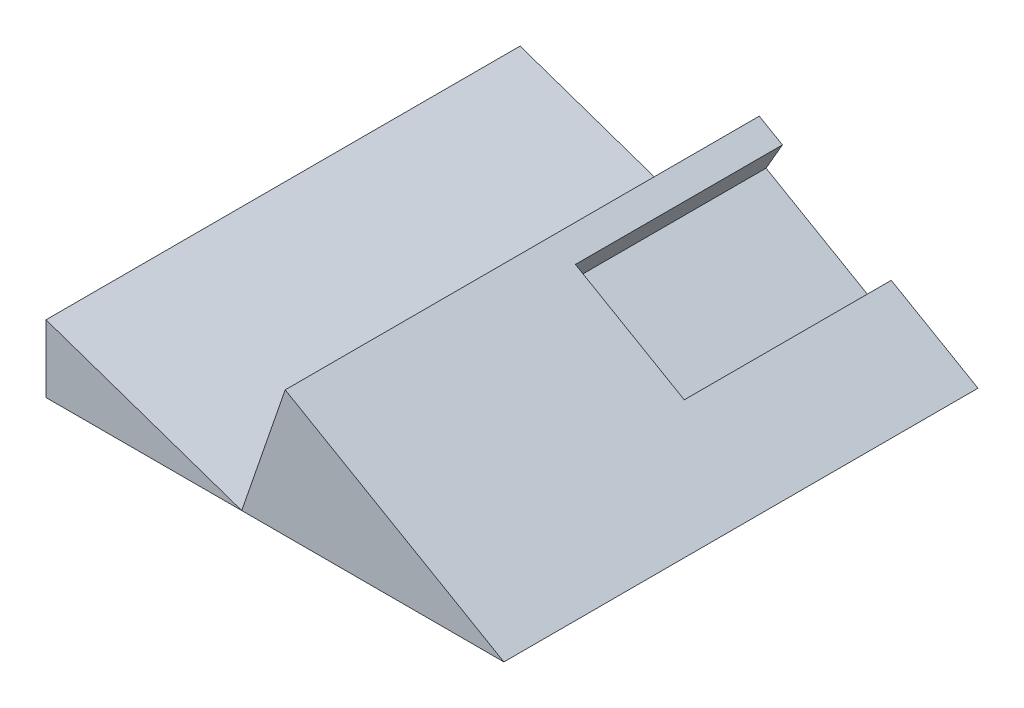
SolidWorks part; units mm, degrees
ref_plane "Front Plane" through (0, 0, 0) normal (0, 0, 1) x (1, 0, 0)
ref_plane "Top Plane" through (0, 0, 0) normal (0, 1, 0) x (1, 0, 0)
ref_plane "Right Plane" through (0, 0, 0) normal (1, 0, 0) x (0, 0, -1)
sketch "Sketch1" plane through (0, 0, 0) normal (0, 1, 0) x (1, 0, 0)
  line L1 (15, -51.5) -> (-15, -51.5)
  line L2 (15, -51.5) -> (15, 51.5)
  line L3 (15, 51.5) -> (-15, 51.5)
  line L4 (-15, -51.5) -> (-15, 51.5)
  line L5 (15, -51.5) -> (-15, 51.5) construction
  line L6 (15, 51.5) -> (-15, -51.5) construction
  point P0 (0, 0)
  dimension "D1" = 103
  dimension "D2" = 30
extrude "Boss-Extrude1" add sketch "Sketch1" along normal blind 2
sketch "Sketch2" plane through (0, 0, 51.5) normal (0, 0, 1) x (1, 0, 0)
  line L0 (15, 2) -> (-35.2295, 31)
  line L1 (0, 2) -> (0, 0)
  line L2 (0, 0) -> (18.4641, 0)
  line L3 (15, 2) -> (18.4641, 0)
  line L8 (-53.5765, 12.0888) -> (-47.0676, 31) construction
  line L9 (-47.0676, 31) -> (-17.7552, 20.9112)
  line L10 (-17.7552, 20.9112) -> (-24.2641, 2) construction
  line L11 (-24.2641, 2) -> (-53.5765, 12.0888)
  line L12 (-15, 2) -> (15, 2) construction
  line L13 (-53.5765, 12.0888) -> (-53.5765, 0)
  line L14 (-24.2641, 2) -> (-49.8195, 2) construction
  line L17 (-15, 2) -> (-15, 0)
  line L18 (-53.5765, 0) -> (-15, 0)
  line L19 (-15, 2) -> (0, 2)
  line L20 (-56.2053, 2) -> (-56.2053, 31) construction
  line L21 (-17.7552, 20.9112) -> (-24.2641, 2)
  line L22 (-56.2053, 31) -> (-14.2536, 31) construction
  dimension "D1" = 30
  dimension "D2" = 20
  dimension "D3" = 31
  dimension "D4" = 29
extrude "Boss-Extrude2" add sketch "Sketch2" against normal blind 103
sketch "Sketch6" plane through (4.616, 7.9952, 0) normal (0.5, 0.866, 0) x (0.866, -0.5, 0)
  line L0 (-21.8321, -11.5) -> (-21.8321, 58.5)
  line L1 (-21.8321, 58.5) -> (-3.0096, 58.5)
  line L2 (-3.0096, 58.5) -> (-3.0096, -11.5)
  line L3 (-3.0096, -11.5) -> (-21.8321, -11.5)
  line L4 (11.9904, -51.5) -> (-25.8321, -51.5) construction
  line L5 (-25.8321, 51.5) -> (-25.8321, -51.5) construction
  line L6 (11.9904, -51.5) -> (11.9904, 51.5) construction
  dimension "D1" = 70
  dimension "D2" = 40
  dimension "D3" = 4
  dimension "D4" = 15
extrude "Cut-Extrude3" cut sketch "Sketch6" against normal blind 4.8964
sketch "Sketch7" plane through (-53.5765, 0, 0) normal (-1, 0, 0) x (0, 0, 1)
  line L0 (-51.5, 20.9112) -> (51.5, 20.9112) construction
  line L1 (-51.5, 0) -> (-19.5, 0)
  line L2 (-51.5, 0) -> (-51.5, 20.9112)
  line L3 (-51.5, 20.9112) -> (-19.5, 20.9112)
  line L4 (-19.5, 0) -> (-19.5, 20.9112)
  line L5 (51.5, 12.0888) -> (51.5, 0) construction
  dimension "D1" = 71
extrude "Cut-Extrude4" cut sketch "Sketch7" against normal blind 73 contours L2 L1 L4 L3
sketch "Sketch8" plane through (0, 0, 51.5) normal (0, 0, 1) x (1, 0, 0)
  line L5 (-73.3631, -28.3791) -> (15, -28.3791)
  line L6 (-73.3631, -28.3791) -> (-73.3631, 2)
  line L7 (-73.3631, 2) -> (15, 2)
  line L8 (15, -28.3791) -> (15, 2)
  point P4 (0, 0)
extrude "Cut-Extrude6" cut sketch "Sketch8" against normal through all both and the other way through all
